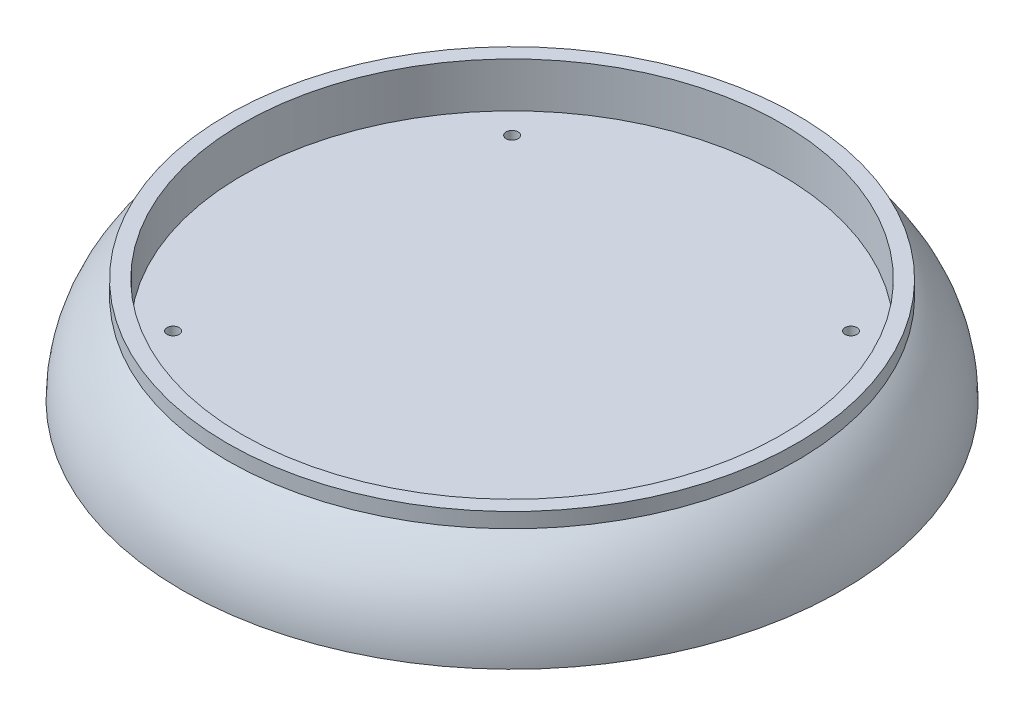
SolidWorks part; units mm, degrees
material "1060 Alloy"
ref_plane "Front Plane" through (0, 0, 0) normal (0, 0, 1) x (1, 0, 0)
ref_plane "Top Plane" through (0, 0, 0) normal (0, 1, 0) x (1, 0, 0)
ref_plane "Right Plane" through (0, 0, 0) normal (1, 0, 0) x (0, 0, -1)
sketch "Sketch1" plane through (0, 0, 0) normal (0, 1, 0) x (1, 0, 0)
  line L0 (0, 0) -> (0, 41.7) construction
  line L3 (-41.7, 0) -> (0, 0) construction
  line L4 (0, 0) -> (-63.6396, 63.6396) construction
  circle A0 centre (0, 0) radius 90 construction
  circle A5 centre (-56.5685, 56.5685) radius 2
  circle A6 centre (-56.5685, -56.5685) radius 2
  circle A7 centre (56.5685, 56.5685) radius 2
  circle A8 centre (56.5685, -56.5685) radius 2
  dimension "D4" = 180
  dimension "D6" = 4
  dimension "D5" = 45
  dimension "D7" = 10
sketch "Sketch2" plane through (0, 0, 0) normal (0, 0, 1) x (1, 0, 0)
  line L0 (90, 0) -> (90, 15)
  line L1 (90, 0) -> (-90, 0) construction
  line L2 (90, 15) -> (95, 15)
  line L3 (95, 15) -> (95, 10)
  line L4 (0, 0) -> (90, 0)
  line L5 (0, 0) -> (0, -20)
  line L6 (0, -99) -> (0, 99) construction
  line L7 (0, -20) -> (110, -20)
  line L8 (90, 0) -> (-90, 0) construction
  arc A0 (110, -20) -> (95, 10) centre (72.5, -20) ccw
  dimension "D1" = 110
  dimension "D2" = 20
  dimension "D3" = 15
  dimension "D4" = 5
  dimension "D5" = 5
revolve "Revolve1" add sketch "Sketch2" angle 360 about L5
extrude "Cut-Extrude1" cut sketch "Sketch1" against normal through all
